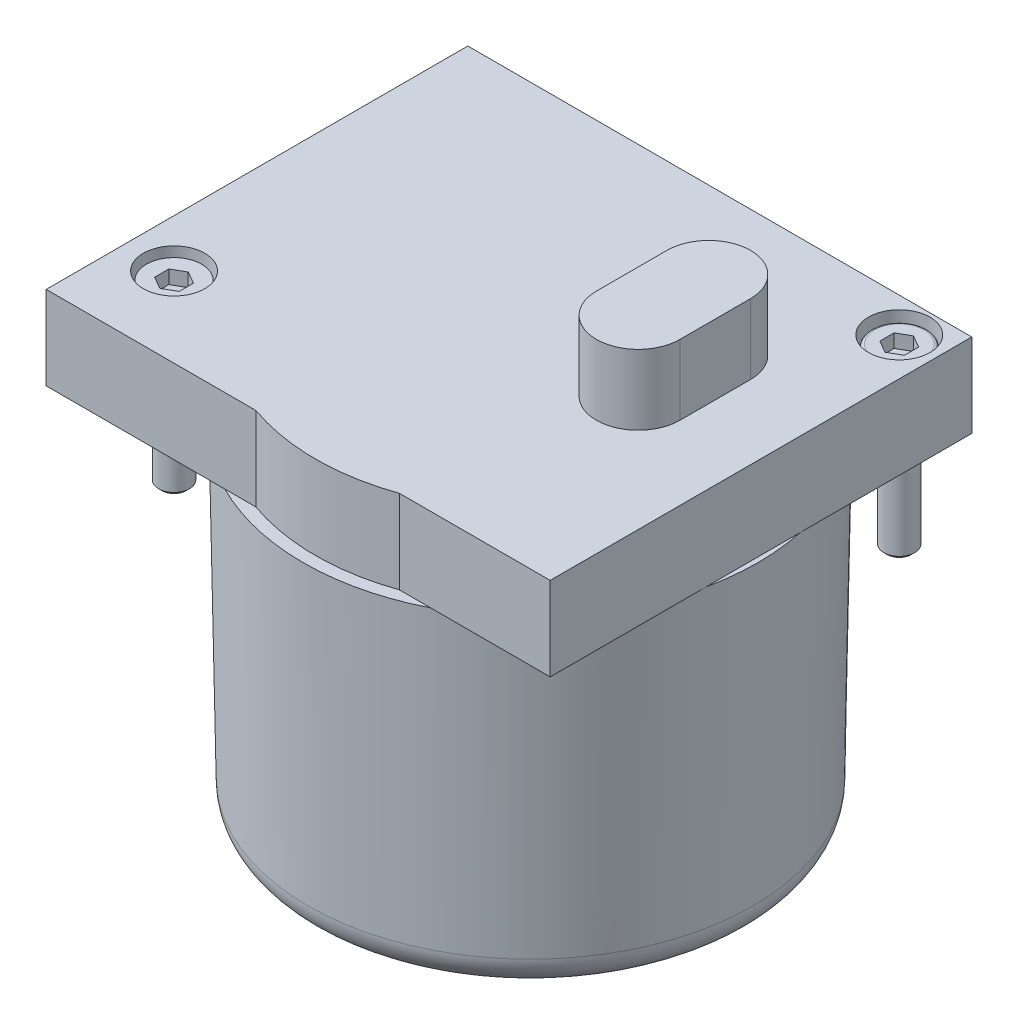
SolidWorks part; units mm, degrees
ref_plane "Front Plane" through (0, 0, 0) normal (0, 0, 1) x (1, 0, 0)
ref_plane "Top Plane" through (0, 0, 0) normal (0, 1, 0) x (1, 0, 0)
ref_plane "Right Plane" through (0, 0, 0) normal (1, 0, 0) x (0, 0, -1)
ref_plane "Plane1" through (0, 0, 0) normal (0, 0, 1) x (1, 0, 0)
sketch "Sketch1" plane through (0, 0, 0) normal (0, 0, 1) x (1, 0, 0)
  line L0 (2.4, 0) -> (19.9, 0)
  line L1 (19.9, 0) -> (19.9, -0.8586)
  line L2 (19.9, -0.8586) -> (19.7586, -1)
  line L3 (19.7586, -1) -> (18.4, -1)
  line L4 (18.4, -1) -> (18.4, -2.5)
  line L5 (18.4, -2.5) -> (19.7586, -2.5)
  line L6 (19.7586, -2.5) -> (19.9, -2.6414)
  line L7 (19.9, -2.6414) -> (19.9, -21)
  line L8 (19.9, -21) -> (2.4, -21)
  line L9 (2.4, -21) -> (2.4, 0)
  line L10 (2.4, -21) -> (2.4, 0) construction
revolve "Revolve1" add sketch "Sketch1" angle 360 about L10
ref_plane "Plane2" through (0, 0, 0) normal (0, 1, 0) x (1, 0, 0)
sketch "Sketch2" plane through (0, 0, 0) normal (0, 1, 0) x (1, 0, 0)
  line L0 (-20.5, 17.8) -> (-20.5, -16.5)
  line L1 (-20.5, -16.5) -> (-3.431, -16.5)
  line L2 (8.231, -16.5) -> (20.5, -16.5)
  line L3 (20.5, -16.5) -> (20.5, 17.8)
  line L4 (20.5, 17.8) -> (-20.5, 17.8)
  arc A0 (-3.431, -16.5) -> (8.231, -16.5) centre (2.4, 0) ccw
extrude "Boss-Extrude1" add sketch "Sketch2" along normal blind 6.8
ref_plane "Plane3" through (0, -21, 0) normal (0, -1, 0) x (-1, 0, 0)
sketch "Sketch3" plane through (0, -21, 0) normal (0, -1, 0) x (-1, 0, 0)
  line L0 (0.6, 18.1031) -> (0.6, 14.6459)
  line L1 (-5.4, 14.6459) -> (-5.4, 18.1031)
  line L2 (-20.5031, 3) -> (-17.0459, 3)
  line L3 (-17.0459, -3) -> (-20.5031, -3)
  line L4 (-5.4, -18.1031) -> (-5.4, -14.6459)
  line L5 (0.6, -14.6459) -> (0.6, -18.1031)
  line L6 (15.7031, -3) -> (12.2459, -3)
  line L7 (12.2459, 3) -> (15.7031, 3)
  arc A0 (15.7031, 3) -> (12.7465, 10.3589) centre (-2.4, 0) ccw
  arc A1 (12.7465, 10.3589) -> (7.9589, 15.1465) centre (10.5754, 12.9754) cw
  arc A2 (7.9589, 15.1465) -> (0.6, 18.1031) centre (-2.4, 0) ccw
  arc A3 (0.6, 14.6459) -> (-5.4, 14.6459) centre (-2.4, 0) ccw
  arc A4 (-5.4, 18.1031) -> (-12.7589, 15.1465) centre (-2.4, 0) ccw
  arc A5 (-12.7589, 15.1465) -> (-17.5465, 10.3589) centre (-15.3754, 12.9754) cw
  arc A6 (-17.5465, 10.3589) -> (-20.5031, 3) centre (-2.4, 0) ccw
  arc A7 (-17.0459, 3) -> (-17.0459, -3) centre (-2.4, 0) ccw
  arc A8 (-20.5031, -3) -> (-17.5465, -10.3589) centre (-2.4, 0) ccw
  arc A9 (-17.5465, -10.3589) -> (-12.7589, -15.1465) centre (-15.3754, -12.9754) cw
  arc A10 (-12.7589, -15.1465) -> (-5.4, -18.1031) centre (-2.4, 0) ccw
  arc A11 (-5.4, -14.6459) -> (0.6, -14.6459) centre (-2.4, 0) ccw
  arc A12 (0.6, -18.1031) -> (7.9589, -15.1465) centre (-2.4, 0) ccw
  arc A13 (7.9589, -15.1465) -> (12.7465, -10.3589) centre (10.5754, -12.9754) cw
  arc A14 (12.7465, -10.3589) -> (15.7031, -3) centre (-2.4, 0) ccw
  arc A15 (12.2459, -3) -> (12.2459, 3) centre (-2.4, 0) ccw
extrude "Cut-Extrude1" cut sketch "Sketch3" against normal blind 15
ref_plane "Plane4" through (0, -21, 0) normal (0, -1, 0) x (-1, 0, 0)
sketch "Sketch4" plane through (0, -21, 0) normal (0, -1, 0) x (-1, 0, 0)
  line L0 (18.8132, -14.1421) -> (4.6711, 0)
  line L1 (4.6711, 0) -> (18.8132, 14.1421)
  line L2 (18.8132, 14.1421) -> (11.7421, 21.2132)
  line L3 (11.7421, 21.2132) -> (-2.4, 7.0711)
  line L4 (-2.4, 7.0711) -> (-16.5421, 21.2132)
  line L5 (-16.5421, 21.2132) -> (-23.6132, 14.1421)
  line L6 (-23.6132, 14.1421) -> (-9.4711, 0)
  line L7 (-9.4711, 0) -> (-23.6132, -14.1421)
  line L8 (-23.6132, -14.1421) -> (-16.5421, -21.2132)
  line L9 (-16.5421, -21.2132) -> (-2.4, -7.0711)
  line L10 (-2.4, -7.0711) -> (11.7421, -21.2132)
  line L11 (11.7421, -21.2132) -> (18.8132, -14.1421)
extrude "Cut-Extrude2" cut sketch "Sketch4" against normal blind 8
ref_plane "Plane5" through (0, 6.8, 0) normal (0, 1, 0) x (1, 0, 0)
sketch "Sketch5" plane through (0, 6.8, 0) normal (0, 1, 0) x (1, 0, 0)
  line L0 (14.5, 0.06) -> (14.5, 5.8)
  line L1 (7.7, 5.8) -> (7.7, 0.06)
  arc A0 (14.5, 5.8) -> (7.7, 5.8) centre (11.1, 5.8) ccw
  arc A1 (7.7, 0.06) -> (14.5, 0.06) centre (11.1, 0.06) ccw
extrude "Boss-Extrude2" add sketch "Sketch5" along normal blind 5.7
ref_plane "Plane6" through (0, 0, -15) normal (0, 0, 1) x (1, 0, 0)
sketch "Sketch6" plane through (0, 0, -15) normal (0, 0, 1) x (1, 0, 0)
  line L0 (17.4, 6.8) -> (19.9, 6.8)
  line L1 (19.9, 6.8) -> (19.9, 3.8)
  line L2 (19.9, 3.8) -> (18.65, 3.8)
  line L3 (18.65, 3.8) -> (18.65, -0.2)
  line L4 (18.65, -0.2) -> (17.4, -0.2)
  line L5 (17.4, -0.2) -> (17.4, 6.8)
  line L6 (17.4, -0.2) -> (17.4, 6.8) construction
revolve "Cut-Revolve1" cut sketch "Sketch6" angle 360 about L6
ref_plane "Plane7" through (0, 0, -15) normal (0, 0, 1) x (1, 0, 0)
sketch "Sketch7" plane through (0, 0, -15) normal (0, 0, 1) x (1, 0, 0)
  line L0 (17.4, 6.15) -> (19.4, 6.15)
  line L1 (19.65, 5.9) -> (19.65, 3.8)
  line L2 (19.65, 3.8) -> (18.65, 3.8)
  line L3 (18.65, 3.8) -> (18.65, -7.924)
  line L4 (18.65, -7.924) -> (18.374, -8.2)
  line L5 (18.374, -8.2) -> (17.4, -8.2)
  line L6 (17.4, -8.2) -> (17.4, 6.15)
  line L7 (17.4, -8.2) -> (17.4, 6.15) construction
  arc A0 (19.4, 6.15) -> (19.65, 5.9) centre (19.4, 5.9) cw
revolve "Revolve2" add sketch "Sketch7" angle 360 about L7
cosmetic thread "Cosmetic Thread1" parameters "D1"=8.2, "D2"=1.948
ref_plane "Plane8" through (0, 6.15, 0) normal (0, 1, 0) x (1, 0, 0)
sketch "Sketch8" plane through (0, 6.15, 0) normal (0, 1, 0) x (1, 0, 0)
  line L0 (16.4, 14.4226) -> (17.4, 13.8453)
  line L1 (17.4, 13.8453) -> (18.4, 14.4226)
  line L2 (18.4, 14.4226) -> (18.4, 15.5774)
  line L3 (18.4, 15.5774) -> (17.4, 16.1547)
  line L4 (17.4, 16.1547) -> (16.4, 15.5774)
  line L5 (16.4, 15.5774) -> (16.4, 14.4226)
extrude "Cut-Extrude3" cut sketch "Sketch8" against normal blind 1.1
ref_plane "Plane9" through (0, 0, 10) normal (0, 0, 1) x (1, 0, 0)
sketch "Sketch9" plane through (0, 0, 10) normal (0, 0, 1) x (1, 0, 0)
  line L0 (-16.6, 6.8) -> (-14.1, 6.8)
  line L1 (-14.1, 6.8) -> (-14.1, 3.8)
  line L2 (-14.1, 3.8) -> (-15.35, 3.8)
  line L3 (-15.35, 3.8) -> (-15.35, -0.2)
  line L4 (-15.35, -0.2) -> (-16.6, -0.2)
  line L5 (-16.6, -0.2) -> (-16.6, 6.8)
  line L6 (-16.6, -0.2) -> (-16.6, 6.8) construction
revolve "Cut-Revolve2" cut sketch "Sketch9" angle 360 about L6
ref_plane "Plane10" through (0, 0, 10) normal (0, 0, 1) x (1, 0, 0)
sketch "Sketch10" plane through (0, 0, 10) normal (0, 0, 1) x (1, 0, 0)
  line L0 (-16.6, 6.15) -> (-14.35, 6.15)
  line L1 (-14.35, 6.15) -> (-14.35, 3.8)
  line L2 (-14.35, 3.8) -> (-15.35, 3.8)
  line L3 (-15.35, 3.8) -> (-15.35, -7.924)
  line L4 (-15.35, -7.924) -> (-15.626, -8.2)
  line L5 (-15.626, -8.2) -> (-16.6, -8.2)
  line L6 (-16.6, -8.2) -> (-16.6, 6.15)
  line L7 (-16.6, -8.2) -> (-16.6, 6.15) construction
revolve "Revolve3" add sketch "Sketch10" angle 360 about L7
cosmetic thread "Cosmetic Thread2" parameters "D1"=8.2, "D2"=1.948
ref_plane "Plane11" through (0, 6.15, 0) normal (0, 1, 0) x (1, 0, 0)
sketch "Sketch11" plane through (0, 6.15, 0) normal (0, 1, 0) x (1, 0, 0)
  line L0 (-17.6, -10.5774) -> (-16.6, -11.1547)
  line L1 (-16.6, -11.1547) -> (-15.6, -10.5774)
  line L2 (-15.6, -10.5774) -> (-15.6, -9.4226)
  line L3 (-15.6, -9.4226) -> (-16.6, -8.8453)
  line L4 (-16.6, -8.8453) -> (-17.6, -9.4226)
  line L5 (-17.6, -9.4226) -> (-17.6, -10.5774)
extrude "Cut-Extrude4" cut sketch "Sketch11" against normal blind 1.1
ref_plane "Plane12" through (0, 0, 0) normal (0, 0, 1) x (1, 0, 0)
sketch "Sketch12" plane through (0, 0, 0) normal (0, 0, 1) x (1, 0, 0)
  line L0 (2.6, -26) -> (2.6, -27)
  line L1 (2.6, -27) -> (17.8467, -27)
  line L2 (20.4851, -24.4061) -> (20.9, 0)
  line L3 (20.9, 0) -> (19.8999, 0)
  line L4 (19.8999, 0) -> (19.4852, -24.3891)
  line L5 (17.8467, -26) -> (2.6, -26)
  line L6 (2.4, -27) -> (2.4, 0) construction
  arc A0 (17.8467, -27) -> (20.4851, -24.4061) centre (17.8467, -24.3612) ccw
  arc A1 (19.4852, -24.3891) -> (17.8467, -26) centre (17.8467, -24.3612) cw
revolve "Revolve4" add sketch "Sketch12" angle 360 about L6
